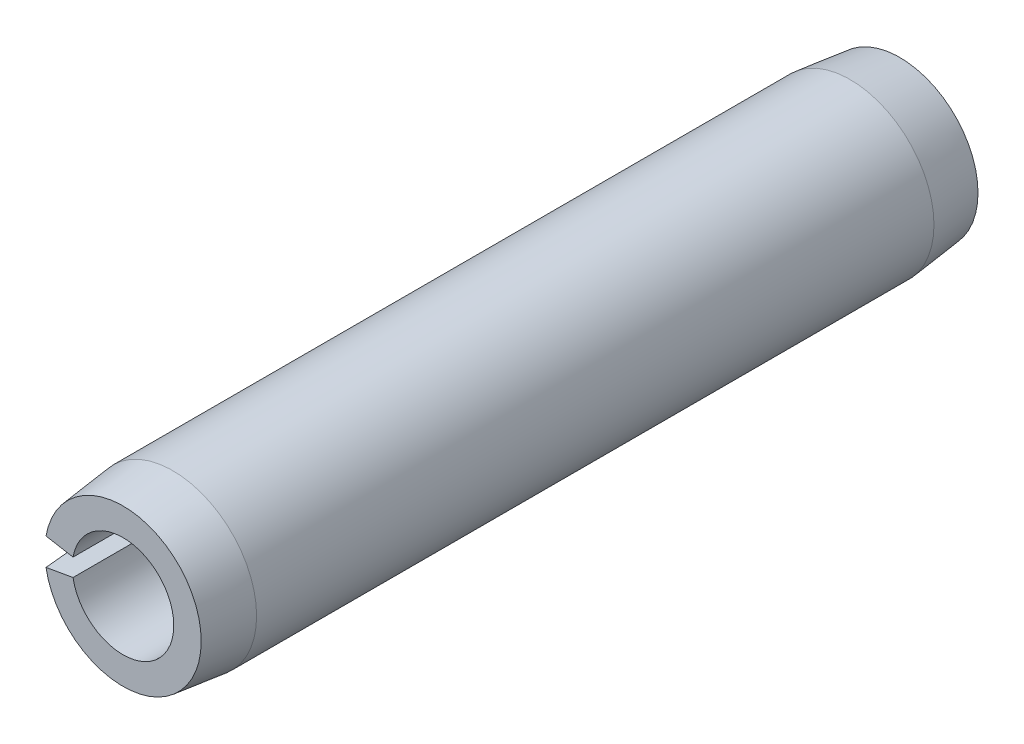
SolidWorks part; units mm, degrees
ref_plane "Front Plane" through (0, 0, 0) normal (0, 0, 1) x (1, 0, 0)
ref_plane "Top Plane" through (0, 0, 0) normal (0, 1, 0) x (1, 0, 0)
ref_plane "Right Plane" through (0, 0, 0) normal (1, 0, 0) x (0, 0, -1)
sketch "Sketch1" plane through (0, 0, 0) normal (0, 0, 1) x (1, 0, 0)
  line L0 (1.2446, 0) -> (2.0574, 0) construction
  line L1 (-2.0261, 0.3573) -> (-1.2257, 0.2161)
  line L2 (-1.2257, -0.2161) -> (-2.0261, -0.3573)
  arc A0 (-2.0261, -0.3573) -> (-2.0261, 0.3573) centre (0, 0) ccw
  arc A1 (-1.2257, -0.2161) -> (-1.2257, 0.2161) centre (0, 0) ccw
  dimension "OD" = 4.1148
  dimension "Wall thickness" = 0.8128
  dimension "D3" = 20
extrude "Extrude1" add sketch "Sketch1" along normal mid plane 19.05
sketch "Sketch2" plane through (0, 0, 0) normal (1, 0, 0) x (0, 0, -1)
  line L0 (0, -2.0574) -> (0, 2.0574) construction
  line L1 (9.525, 0) -> (-9.525, 0) construction
  line L2 (9.525, -1.2446) -> (9.525, 1.2446) construction
  line L3 (9.525, 2.0574) -> (-9.525, 2.0574) construction
  line L4 (9.525, 2.0574) -> (9.525, 1.9177)
  line L5 (9.525, 1.9177) -> (8.3058, 2.0574)
  line L6 (8.3058, 2.0574) -> (9.525, 2.0574)
  line L7 (9.525, -2.0574) -> (9.525, 2.0574) construction
  line L8 (-8.3058, 2.0574) -> (-9.525, 2.0574)
  line L9 (-9.525, 1.9177) -> (-8.3058, 2.0574)
  line L10 (-9.525, 2.0574) -> (-9.525, 1.9177)
  line L11 (8.3058, -2.0574) -> (9.525, -2.0574) construction
  line L12 (9.525, -1.9177) -> (8.3058, -2.0574) construction
  line L13 (9.525, -2.0574) -> (9.525, -1.9177) construction
  dimension "B" = 3.8354
  dimension "Chamfer max" = 1.2192
revolve "Cut-Revolve1" cut sketch "Sketch2" angle 360 about L1
sketch "Sketch3" plane through (0, 0, 0) normal (0, 0, 1) x (1, 0, 0)
  line L0 (1.2446, 0) -> (2.0574, 0) construction
  line L1 (1.2446, 0) -> (2.0574, 0)
  circle A0 centre (0, 0) radius 2.0574
  circle A1 centre (0, 0) radius 1.2446
  arc A2 (-2.0261, -0.3573) -> (-2.0261, 0.3573) centre (0, 0) ccw construction
  arc A3 (-1.2257, -0.2161) -> (-1.2257, 0.2161) centre (0, 0) ccw construction
